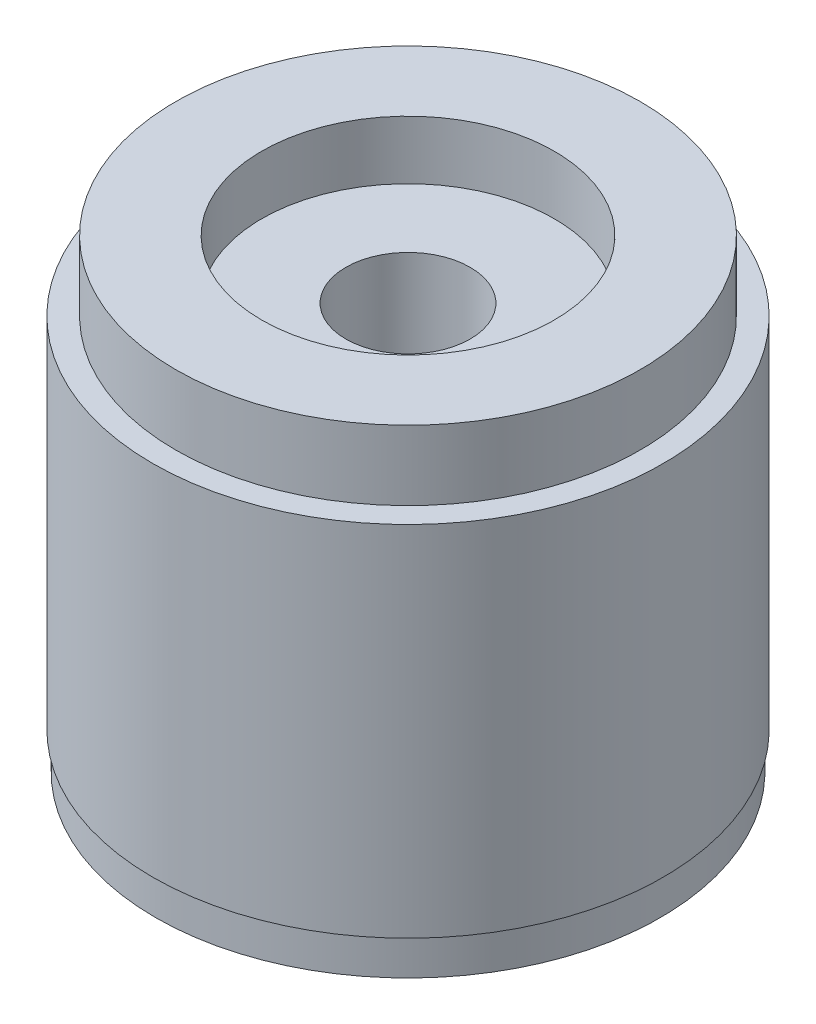
SolidWorks part; units mm, degrees
ref_plane "Front Plane" through (0, 0, 0) normal (0, 0, 1) x (1, 0, 0)
ref_plane "Top Plane" through (0, 0, 0) normal (0, 1, 0) x (1, 0, 0)
ref_plane "Right Plane" through (0, 0, 0) normal (1, 0, 0) x (0, 0, -1)
sketch "Sketch1" plane through (0, 0, 0) normal (0, 1, 0) x (1, 0, 0)
  circle A0 centre (0, 0) radius 34.91
extrude "Boss-Extrude1" add sketch "Sketch1" along normal blind 63.5 separate body
sketch "Sketch2" plane through (0, 0, 0) normal (0, -1, 0) x (1, 0, 0)
  circle A0 centre (0, 0) radius 34.5
extrude "Cut-Extrude1" cut sketch "Sketch2" against normal blind 5 flip side to cut
sketch "Sketch3" plane through (0, 63.5, 0) normal (0, 1, 0) x (1, 0, 0)
  circle A0 centre (0, 0) radius 31.75
extrude "Cut-Extrude2" cut sketch "Sketch3" against normal blind 9.52 flip side to cut
sketch "Sketch4" plane through (0, 63.5, 0) normal (0, 1, 0) x (1, 0, 0)
  circle A0 centre (0, 0) radius 20
extrude "Cut-Extrude3" cut sketch "Sketch4" against normal blind 8
sketch "Sketch5" plane through (0, 0, 0) normal (0, -1, 0) x (1, 0, 0)
  circle A0 centre (0, 0) radius 8.5
extrude "Cut-Extrude4" cut sketch "Sketch5" against normal through all
sketch "Sketch6" plane through (0, 0, 0) normal (0, -1, 0) x (1, 0, 0)
  circle A0 centre (0, 0) radius 14.5
extrude "Cut-Extrude5" cut sketch "Sketch6" against normal blind 5
